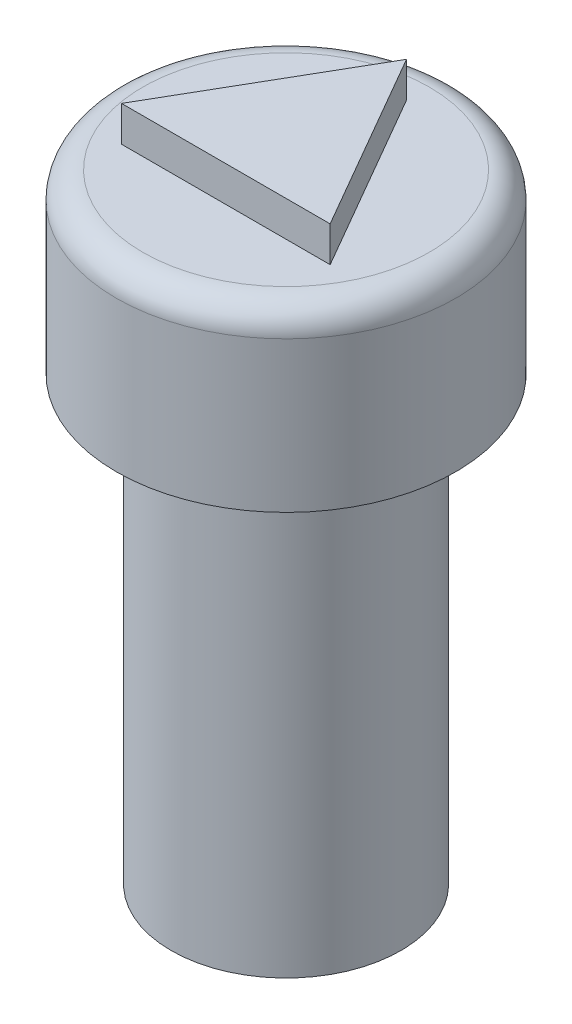
SolidWorks part; units mm, degrees
ref_plane "Front Plane" through (0, 0, 0) normal (0, 0, 1) x (1, 0, 0)
ref_plane "Top Plane" through (0, 0, 0) normal (0, 1, 0) x (1, 0, 0)
ref_plane "Right Plane" through (0, 0, 0) normal (1, 0, 0) x (0, 0, -1)
sketch "Sketch1" plane through (0, 0, 0) normal (0, 1, 0) x (1, 0, 0)
  circle A0 centre (0, 0) radius 3.25
  dimension "D1" = 6.5
extrude "Boss-Extrude1" add sketch "Sketch1" along normal blind 12.5 contours A0
sketch "Sketch2" plane through (0, 0, 0) normal (0, -1, 0) x (1, 0, 0)
  circle A1 centre (0, 0) radius 1.75
  dimension "D1" = 3.5
extrude "Cut-Extrude1" cut sketch "Sketch2" against normal blind 2.5
sketch "Sketch6" plane through (0, 12.5, 0) normal (0, 1, 0) x (1, 0, 0)
  circle A0 centre (0, 0) radius 4.8
  dimension "D1" = 9.6
extrude "Boss-Extrude2" add sketch "Sketch6" along normal blind 5 contours A0
sketch "Sketch7" plane through (0, 17.5, 0) normal (0, 1, 0) x (1, 0, 0)
  line L1 (2.95, -1.7032) -> (0, 3.4064)
  line L2 (0, 3.4064) -> (-2.95, -1.7032)
  line L3 (-2.95, -1.7032) -> (2.95, -1.7032)
  circle A0 centre (0, 0) radius 1.7032 construction
  dimension "D1" = 5.9
  dimension "D2" = 5.9
extrude "Boss-Extrude5" add sketch "Sketch7" along normal blind 1
fillet "Fillet1" radius 0.75 1 edges at (0, 17.5, 4.8)
